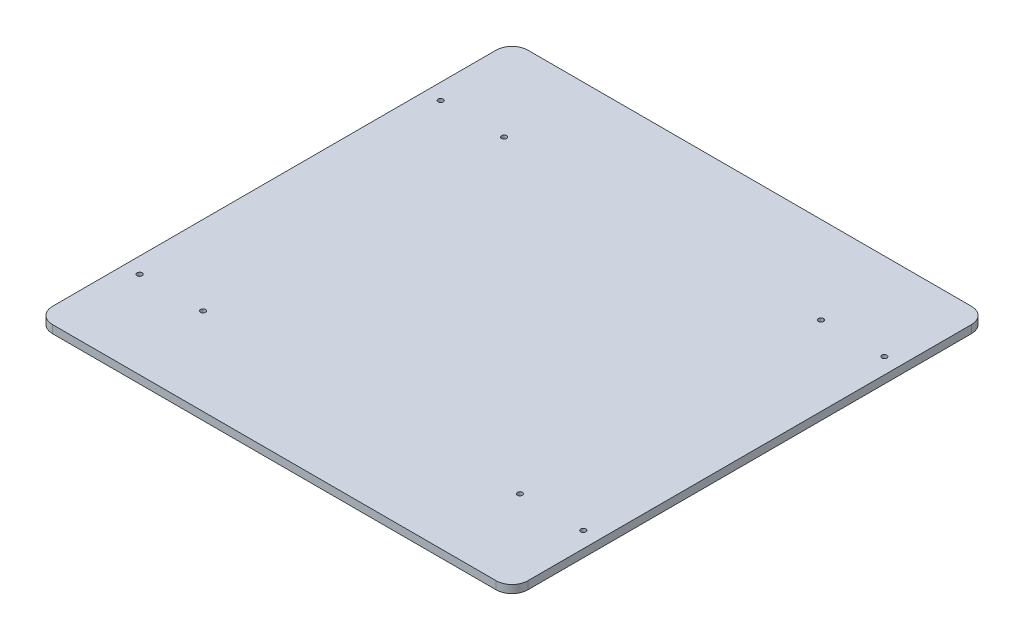
SolidWorks part; units mm, degrees
ref_plane "Plan de face" through (0, 0, 0) normal (0, 0, 1) x (1, 0, 0)
ref_plane "Plan de dessus" through (0, 0, 0) normal (0, 1, 0) x (1, 0, 0)
ref_plane "Plan de droite" through (0, 0, 0) normal (1, 0, 0) x (0, 0, -1)
sketch "Esquisse1" plane through (0, 0, 0) normal (0, 1, 0) x (1, 0, 0)
  line L1 (-150, -150) -> (150, -150)
  line L2 (-150, -150) -> (-150, 150)
  line L3 (-150, 150) -> (150, 150)
  line L4 (150, -150) -> (150, 150)
  line L5 (-150, -150) -> (150, 150) construction
  line L6 (-150, 150) -> (150, -150) construction
  point P0 (0, 0)
  dimension "D1" = 300
  dimension "D2" = 300
extrude "Boss.-Extru.1" add sketch "Esquisse1" along normal blind 5
fillet "Congé1" radius 10 4 edges at (-150, 2.5, -150) (150, 2.5, -150) (150, 2.5, 150) (-150, 2.5, 150)
sketch "Esquisse2" plane through (0, 0, 0) normal (0, -1, 0) x (1, 0, 0)
  line L0 (-140, 95) -> (-100, 95) construction
  circle A0 centre (-140, 95) radius 1.6
  circle A1 centre (-100, 95) radius 1.6
  point P4 (-120, 95)
  dimension "D1" = 3.2
  dimension "D2" = 40
  dimension "D3" = 120
  dimension "D4" = 95
extrude "Enlèv. mat.-Extru.1" cut sketch "Esquisse2" against normal through all
pattern_linear "Répétition linéaire1" count 2 spacing 240 along (1, 0, 0) count 2 spacing 190 along (0, 0, -1) of "Enlèv. mat.-Extru.1"
